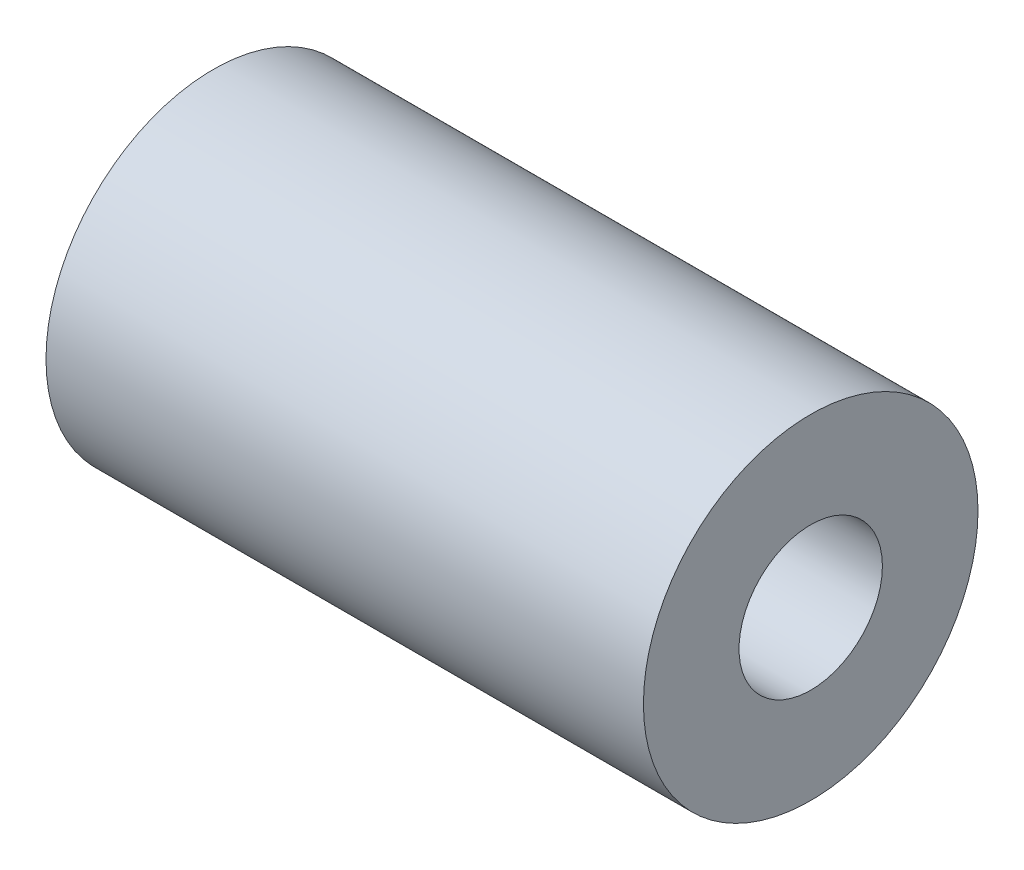
SolidWorks part; units mm, degrees
ref_plane "前视基准面" through (0, 0, 0) normal (0, 0, 1) x (1, 0, 0)
ref_plane "上视基准面" through (0, 0, 0) normal (0, 1, 0) x (1, 0, 0)
ref_plane "右视基准面" through (0, 0, 0) normal (1, 0, 0) x (0, 0, -1)
sketch "草图1" plane through (0, 0, 0) normal (1, 0, 0) x (0, 0, -1)
  circle A0 centre (0, 0) radius 1.5
  circle A1 centre (0, 0) radius 3.5
  dimension "D1" = 3
  dimension "D2" = 7
extrude "凸台-拉伸1" add sketch "草图1" along normal blind 12.5
